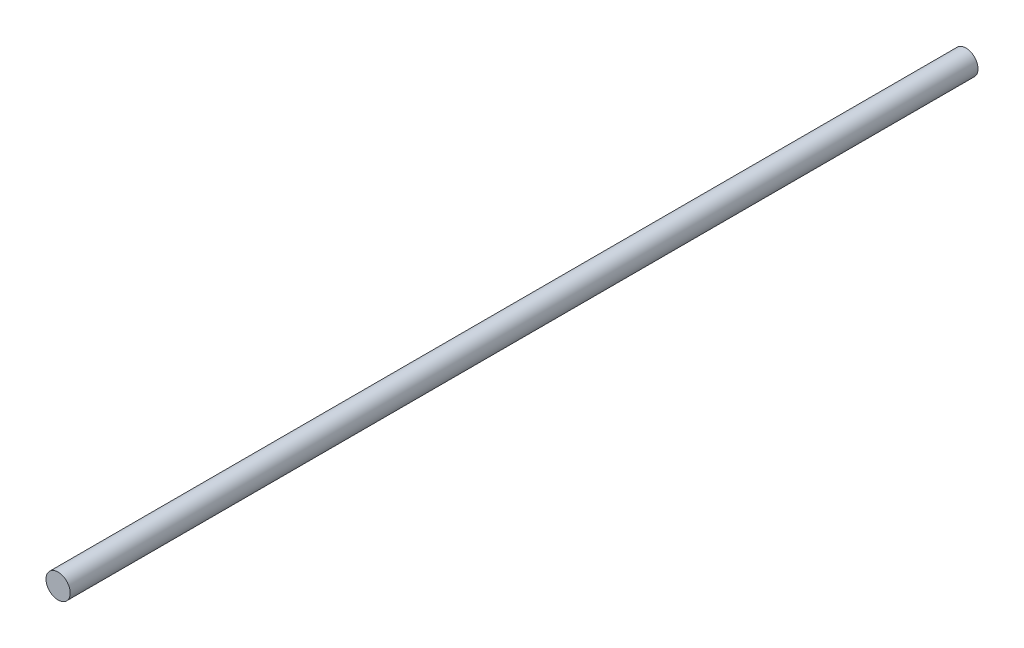
SolidWorks part; units mm, degrees
ref_plane "Front Plane" through (0, 0, 0) normal (0, 0, 1) x (1, 0, 0)
ref_plane "Top Plane" through (0, 0, 0) normal (0, 1, 0) x (1, 0, 0)
ref_plane "Right Plane" through (0, 0, 0) normal (1, 0, 0) x (0, 0, -1)
sketch "Sketch1" plane through (0, 0, 0) normal (0, 0, 1) x (1, 0, 0)
  circle A0 centre (0, 0) radius 2
extrude "Boss-Extrude1" add sketch "Sketch1" along normal blind 150
